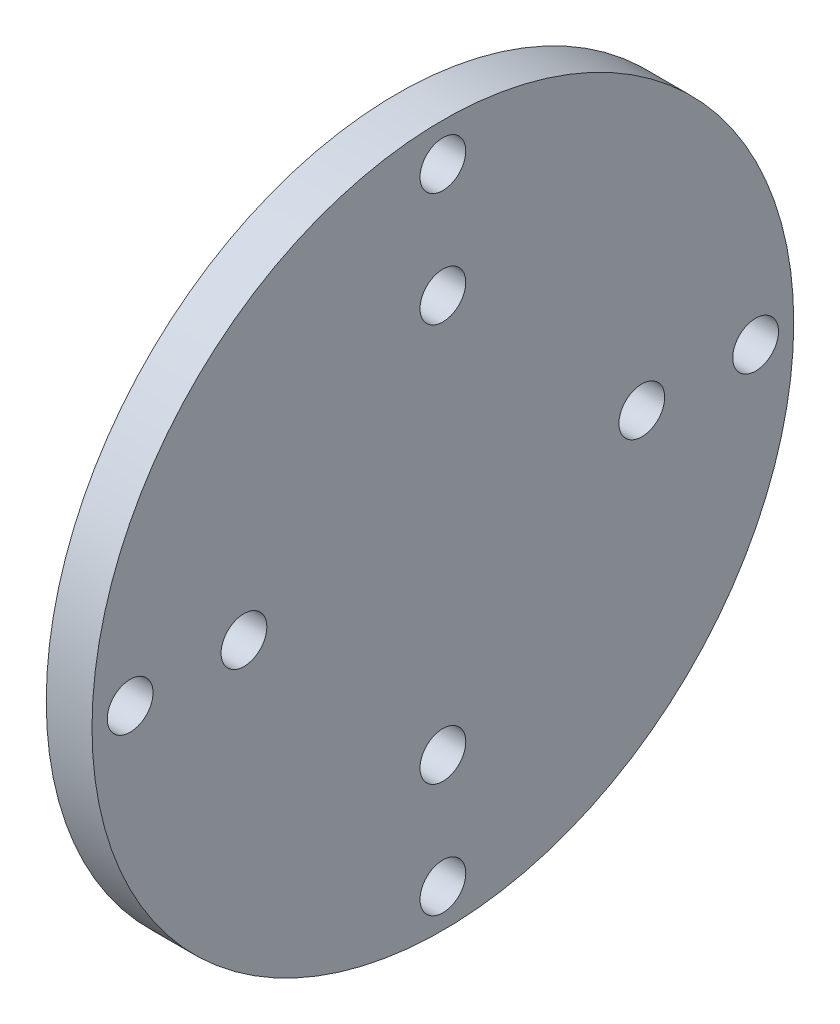
SolidWorks part; units mm, degrees
ref_plane "Front Plane" through (0, 0, 0) normal (0, 0, 1) x (1, 0, 0)
ref_plane "Top Plane" through (0, 0, 0) normal (0, 1, 0) x (1, 0, 0)
ref_plane "Right Plane" through (0, 0, 0) normal (1, 0, 0) x (0, 0, -1)
sketch "Sketch1" plane through (0, 0, 0) normal (1, 0, 0) x (0, 0, -1)
  line L0 (0, -6.5) -> (0, -1.5) construction
  circle A2 centre (0, 16.5) radius 23
  circle A10 centre (0, -4) radius 1.5
  circle A11 centre (0, 3.46) radius 1.5
  circle A12 centre (-13.04, 16.5) radius 1.5
  circle A13 centre (-20.5, 16.5) radius 1.5
  circle A14 centre (0, 29.54) radius 1.5
  circle A15 centre (0, 37) radius 1.5
  circle A16 centre (13.04, 16.5) radius 1.5
  circle A17 centre (20.5, 16.5) radius 1.5
  point P27 (0, 16.5)
  dimension "D1" = 46
  dimension "D4" = 3
  dimension "D3" = 5
  dimension "D5" = 2
  dimension "D6" = 4
extrude "Boss-Extrude1" add sketch "Sketch1" along normal blind 3
